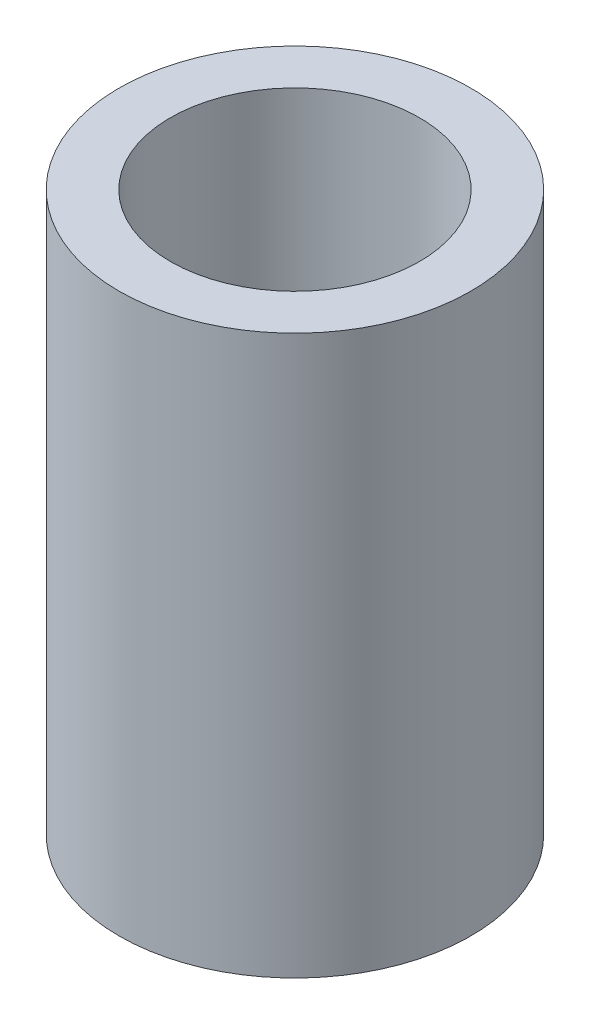
SolidWorks part; units mm, degrees
ref_plane "Front Plane" through (0, 0, 0) normal (0, 0, 1) x (1, 0, 0)
ref_plane "Top Plane" through (0, 0, 0) normal (0, 1, 0) x (1, 0, 0)
ref_plane "Right Plane" through (0, 0, 0) normal (1, 0, 0) x (0, 0, -1)
sketch "Sketch1" plane through (0, 0, 0) normal (0, 1, 0) x (1, 0, 0)
  circle A0 centre (0, 0) radius 4.25
  circle A1 centre (0, 0) radius 6
  dimension "D1" = 8.5
  dimension "D2" = 12
extrude "Boss-Extrude1" add sketch "Sketch1" along normal blind 19.05
